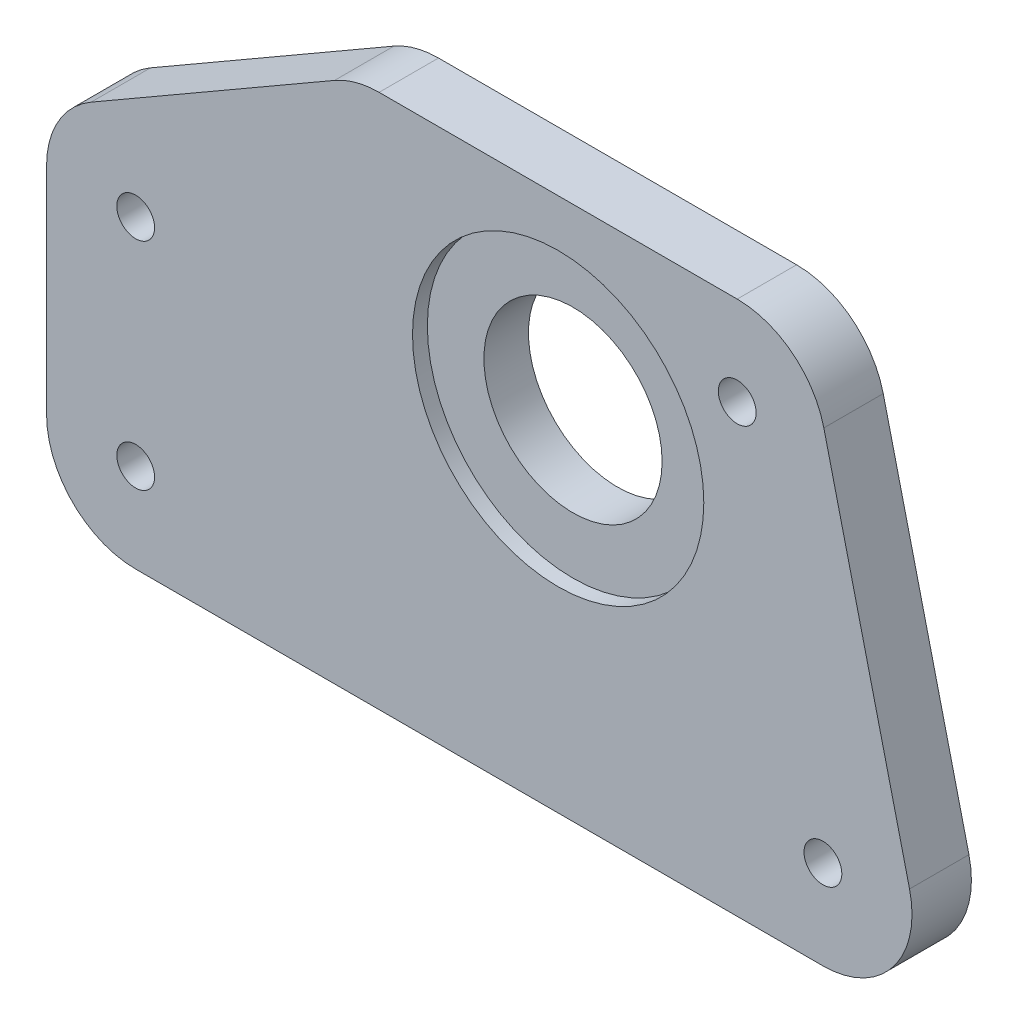
SolidWorks part; units mm, degrees
ref_plane "Front Plane" through (0, 0, 0) normal (0, 0, 1) x (1, 0, 0)
ref_plane "Top Plane" through (0, 0, 0) normal (0, 1, 0) x (1, 0, 0)
ref_plane "Right Plane" through (0, 0, 0) normal (1, 0, 0) x (0, 0, -1)
sketch "Sketch1" plane through (0, 0, 0) normal (0, 0, 1) x (1, 0, 0)
  line L0 (-49.9251, 4.3371) -> (-23.9023, 19.3614)
  line L1 (-19.1398, 20.6375) -> (19.1398, 20.6375)
  line L2 (-54.6876, -3.9118) -> (-54.6876, -26.9875)
  line L3 (-45.1626, -36.5125) -> (28.3034, -36.5125)
  line L5 (28.4007, 13.3399) -> (37.5643, -24.7601)
  circle A0 centre (0, 0) radius 9.525
  arc A1 (28.4007, 13.3399) -> (19.1398, 20.6375) centre (19.1398, 11.1125) ccw
  arc A2 (-19.1398, 20.6375) -> (-23.9023, 19.3614) centre (-19.1398, 11.1125) ccw
  arc A3 (-54.6876, -3.9118) -> (-49.9251, 4.3371) centre (-45.1626, -3.9118) cw
  arc A4 (-54.6876, -26.9875) -> (-45.1626, -36.5125) centre (-45.1626, -26.9875) ccw
  arc A5 (28.3034, -36.5125) -> (37.5643, -24.7601) centre (28.3034, -26.9875) ccw
  point P4 (0, 20.6375)
  dimension "D1" = 19.05
  dimension "D3" = 36.5125
  dimension "D4" = 23.0757
  dimension "D2" = 9.525
  dimension "D5" = 150
  dimension "D6" = 30.0485
  dimension "D7" = 38.2797
  dimension "D8" = 39.1865
extrude "Boss-Extrude1" add sketch "Sketch1" along normal blind 6.35 contours L3 A5 L5 A1 L1 A2 L0 A3 L2 A4 A0
sketch "Sketch2" plane through (0, 0, 0) normal (0, 0, -1) x (-1, 0, 0)
  circle A0 centre (0, 0) radius 15.5702
  dimension "D1" = 31.1404
extrude "Cut-Extrude1" [suppressed] cut sketch "Sketch2" against normal blind 1.5875
sketch "Sketch6" plane through (0, 0, 6.35) normal (0, 0, 1) x (1, 0, 0)
  circle A0 centre (0, 0) radius 15.5702
  dimension "D1" = 31.1404
extrude "Cut-Extrude2" cut sketch "Sketch6" against normal blind 1.5875 contours A0
hole_wizard "Tap Drill for #10-32 Tap1" positions "Sketch5" profile "Sketch4" hole size "#10-32" standard "ANSI Inch" end condition through all
sketch "Sketch5" plane through (0, 0, 0) normal (0, 0, -1) x (-1, 0, 0)
  arc A0 (-37.5643, -24.7601) -> (-28.3034, -36.5125) centre (-28.3034, -26.9875) ccw construction
  arc A1 (45.1626, -36.5125) -> (54.6876, -26.9875) centre (45.1626, -26.9875) ccw construction
  arc A2 (54.6876, -3.9118) -> (49.9251, 4.3371) centre (45.1626, -3.9118) ccw construction
  arc A3 (-19.1398, 20.6375) -> (-28.4007, 13.3399) centre (-19.1398, 11.1125) ccw construction
  point P0 (-28.3034, -26.9875)
  point P2 (-19.1398, 11.1125)
  point P4 (45.1626, -3.9118)
  point P6 (45.1626, -26.9875)
sketch "Sketch4" plane through (28.3034, -26.9875, 0) normal (1, 0, 0) x (0, 1, 0)
  line L0 (0, 0) -> (0, 6.35)
  line L1 (0, 6.35) -> (2.0193, 6.35)
  line L2 (2.0193, 6.35) -> (2.0193, 0)
  line L5 (2.0193, 0) -> (0, 0)
  line L11 (0, -6.35) -> (0, 107.95) construction
  dimension "Thru Hole Dia." = 4.0386
  dimension "Thru Hole Depth" = 6.35
